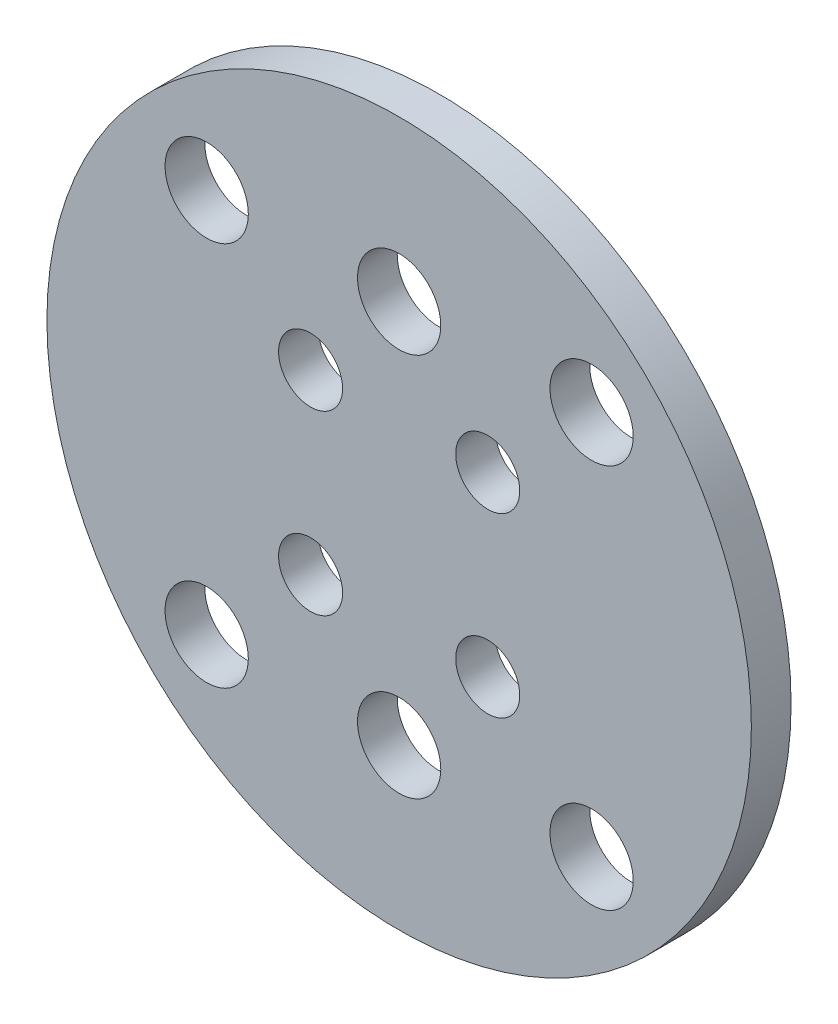
SolidWorks part; units mm, degrees
material "Teak"
ref_plane "Front Plane" through (0, 0, 0) normal (0, 0, 1) x (1, 0, 0)
ref_plane "Top Plane" through (0, 0, 0) normal (0, 1, 0) x (1, 0, 0)
ref_plane "Right Plane" through (0, 0, 0) normal (1, 0, 0) x (0, 0, -1)
sketch "Sketch1" plane through (0, 0, 0) normal (0, 0, 1) x (1, 0, 0)
  line L0 (0, 0) -> (27.5, 0) construction
  line L1 (27.5, 0) -> (0, -27.5) construction
  line L2 (0, -27.5) -> (0, 0) construction
  line L3 (0, 0) -> (13.75, -13.75) construction
  circle A0 centre (0, 0) radius 27.5
  circle A1 centre (-6.9148, 6.9148) radius 2.5
  circle A2 centre (6.9148, 6.9148) radius 2.5
  circle A3 centre (6.9148, -6.9148) radius 2.5
  circle A4 centre (-6.9148, -6.9148) radius 2.5
  circle A5 centre (15.026, -15.026) radius 3.25
  circle A6 centre (-15.026, -15.026) radius 3.25
  circle A7 centre (-15.026, 15.026) radius 3.25
  circle A8 centre (15.026, 15.026) radius 3.25
  circle A9 centre (0, -15) radius 3.25
  circle A10 centre (0, 15) radius 3.25
  point P14 (0, 0)
  point P26 (0, 0)
  dimension "D1" = 55
  dimension "D2" = 5
  dimension "D6" = 6.5
  dimension "D10" = 6.5
  dimension "D4" = 19.558
  dimension "D5" = 0
  dimension "D8" = 42.5
  dimension "D9" = 0
  dimension "D11" = 30
  dimension "D3" = 4
  dimension "D7" = 4
extrude "Boss-Extrude1" add sketch "Sketch1" along normal blind 3.1
equation "\"thick\" = 3.1mm"
equation "\"small_bearing_outer\"=12.9mm"
equation "\"servo1_L\"=40.7mm"
equation "\"servo1_W\"=20.5mm"
equation "\"servo1_H\"=43.5mm"
equation "\"servo1_hL\"=49mm"
equation "\"servo1_hW\"=10mm"
equation "\"servo1_H2\"=27mm"
equation "\"large_bearing_inner\"=2.75in"
equation "\"large_bearing_outer\"=4.75in"
equation "\"large_bearing_thick\"=3/8in"
equation "\"large_bearing_h1\"=3.25in"
equation "\"large_bearing_h2\"=4.25in"
